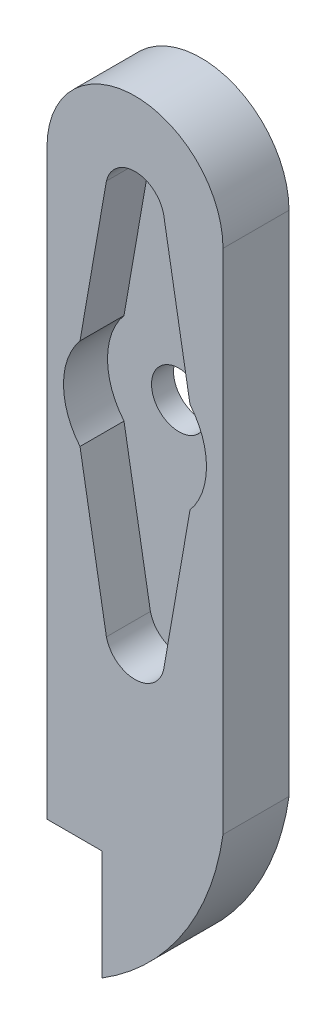
SolidWorks part; units mm, degrees
ref_plane "前基準面" through (0, 0, 0) normal (0, 0, 1) x (1, 0, 0)
ref_plane "上基準面" through (0, 0, 0) normal (0, 1, 0) x (1, 0, 0)
ref_plane "右基準面" through (0, 0, 0) normal (1, 0, 0) x (0, 0, -1)
sketch "草圖1" plane through (0, 0, 0) normal (0, 0, 1) x (1, 0, 0)
  line L1 (0, -55) -> (0, 55) construction
  line L2 (-5, 4.15) -> (-2.6, 17.9428)
  line L3 (2.6, 17.9428) -> (5, 4.15)
  line L4 (2.6, -17.9428) -> (5, -4.15)
  line L5 (-5, -4.15) -> (-2.6, -17.9428)
  line L6 (55, 0) -> (-55, 0) construction
  line L12 (3.5805, 18.1413) -> (3.615, 17.9428)
  line L14 (-5.9852, 4.3214) -> (-3.5805, 18.1413) construction
  line L15 (3.5805, 18.1413) -> (5.9852, 4.3214) construction
  line L17 (3.615, 17.9428) -> (-3.615, 17.9428)
  line L18 (8, 17.9428) -> (8, -24.9346)
  line L20 (-8, 17.9428) -> (-8, -18.1413)
  line L21 (-3.615, 17.9428) -> (-3.5805, 18.1413)
  line L29 (-8, -18.1413) -> (-8, -28.2067)
  line L31 (8, -28.2067) -> (8, -24.9346)
  line L33 (-8, -35) -> (-8, -24.9346)
  line L34 (-3, -35) -> (-3, -45)
  line L35 (-8, -35) -> (-3, -35)
  arc A0 (-4.9993, 4.1542) -> (-4.9993, -4.1542) centre (0, 0) ccw
  arc A3 (-2.6, 17.9428) -> (2.6, 17.9428) centre (0, 17.3284) cw
  arc A4 (-2.6, -17.9428) -> (2.6, -17.9428) centre (0, -17.3284) ccw
  arc A5 (4.9993, -4.1542) -> (4.9993, 4.1542) centre (0, 0) ccw
  arc A12 (8, 17.9428) -> (-8, 17.9428) centre (0, 17.9428) ccw
  arc A14 (-3.5805, 18.1413) -> (3.5805, 18.1413) centre (0, 17.3284) cw construction
  arc A17 (8, -28.2067) -> (-3, -45) centre (-15.4438, -24.8497) cw
  point P10 (0, 20)
  dimension "D1" = 5
  dimension "D2" = 14
  dimension "D3" = 14
  dimension "D9" = 13
  dimension "D4" = 5
  dimension "D5" = 2.6
  dimension "D6" = 20
  dimension "D7" = 2.6
  dimension "D10" = 1
extrude "填料-伸長1" add sketch "草圖1" along normal blind 6
sketch "草圖2" plane through (0, 0, 0) normal (0, 0, 1) x (1, 0, 0)
  line L1 (-6.6467, 20.4102) -> (7.0328, 20.4102)
  line L2 (-6.6467, 20.4102) -> (-6.6467, -20.6283)
  line L3 (-6.6467, -20.6283) -> (7.0328, -20.6283)
  line L4 (7.0328, 20.4102) -> (7.0328, -20.6283)
  circle A0 centre (0, 0) radius 2.5
extrude "填料-伸長2" add sketch "草圖2" along normal blind 2
